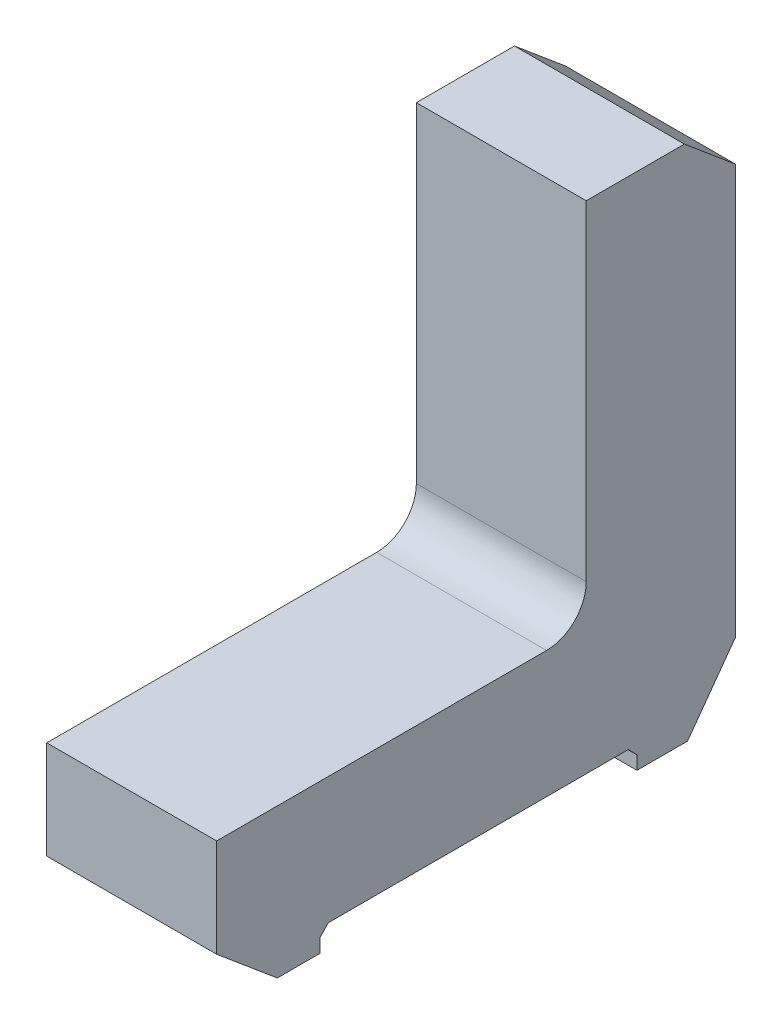
SolidWorks part; units mm, degrees
ref_plane "Front Plane" through (0, 0, 0) normal (0, 0, 1) x (1, 0, 0)
ref_plane "Top Plane" through (0, 0, 0) normal (0, 1, 0) x (1, 0, 0)
ref_plane "Right Plane" through (0, 0, 0) normal (1, 0, 0) x (0, 0, -1)
sketch "Sketch2" plane through (0, 0, 0) normal (1, 0, 0) x (0, 0, -1)
  line L0 (-110.6805, 0) -> (-110.6805, -32.9212)
  line L1 (-110.6805, -32.9212) -> (-90.3268, -50)
  line L2 (-90.3268, -50) -> (47.3112, -50)
  line L3 (-110.6805, 0) -> (0, 0)
  line L4 (13.3195, 13.3195) -> (13.3195, 124)
  line L5 (13.3195, 124) -> (46.2407, 124)
  line L6 (46.2407, 124) -> (63.3195, 109.6692)
  line L7 (63.3195, 109.6692) -> (63.3195, -27.9688)
  line L8 (47.3112, -50) -> (63.3195, -27.9688)
  arc A2 (0, 0) -> (13.3195, 13.3195) centre (0, 13.3195) ccw
  point P14 (13.3195, 76.2495)
  point P18 (-63.7303, 0)
  dimension "D2" = 140
  dimension "D1" = 124
  dimension "D3" = 50
  dimension "D4" = 50
extrude "Boss-Extrude1" add sketch "Sketch2" along normal blind 57
fillet "Fillet1" [suppressed] radius 10
fillet "Fillet2" [suppressed] radius 7.5
sketch "Sketch3" plane through (57, 0, 0) normal (1, 0, 0) x (0, 0, -1)
  line L0 (-76.0759, -50) -> (-76.0759, -45.5)
  line L1 (30.3307, -50) -> (30.3307, -45.5)
  line L2 (-73.2065, -42.5) -> (27.4613, -42.5)
  line L3 (-90.3268, -50) -> (47.3112, -50) construction
  line L4 (-76.0759, -45.5) -> (-73.2065, -42.5)
  line L5 (27.4613, -42.5) -> (30.3307, -45.5)
  line M14 (-90.3268, -50) -> (47.3112, -50)
  dimension "D2" = 7.5
extrude "Cut-Extrude1" cut sketch "Sketch3" against normal through all contours L5 L2 L4 L0 L1 M14
equation "\"w_claw\"= 80mm"
equation "\"h_cube\"= 57mm"
equation "\"dx_claws\"= 124mm"
equation "\"dy_claws\"= 124mm"
equation "\"w_motorA\"= 40mm"
equation "\"l_motorA\"= 20mm"
equation "\"w_motorB\"= 40mm"
equation "\"l_motorB\"= 20mm"
equation "\"D1@Boss-Extrude1\"=\"h_cube\""
equation "\"D1@Sketch2\"=\"dy_claws\""
